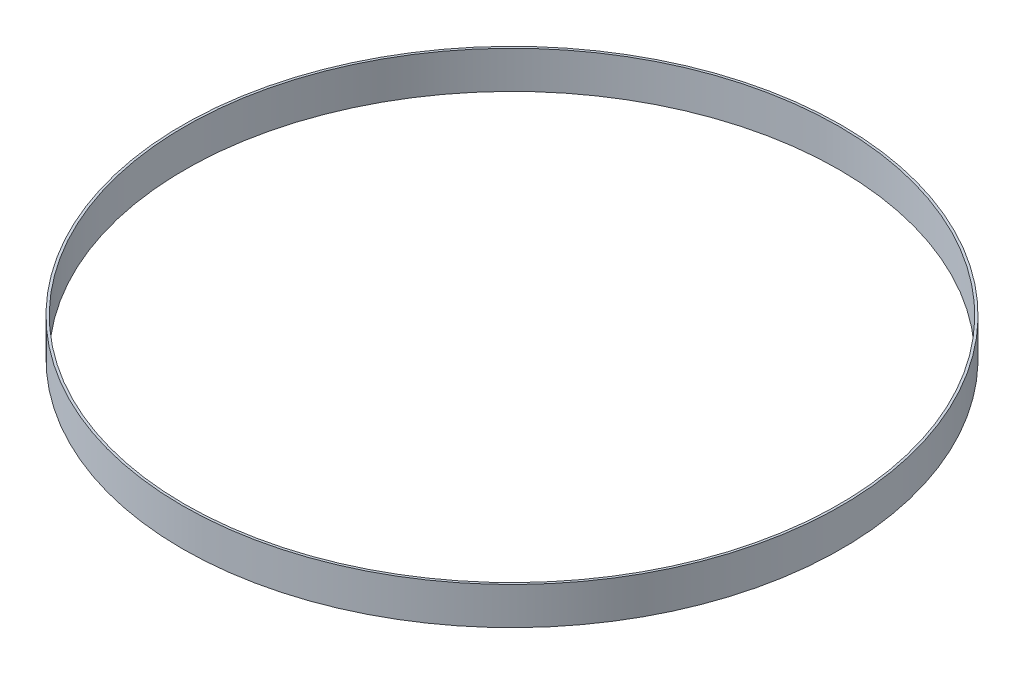
SolidWorks part; units mm, degrees
ref_plane "Front Plane" through (0, 0, 0) normal (0, 0, 1) x (1, 0, 0)
ref_plane "Top Plane" through (0, 0, 0) normal (0, 1, 0) x (1, 0, 0)
ref_plane "Right Plane" through (0, 0, 0) normal (1, 0, 0) x (0, 0, -1)
sketch "Sketch2" plane through (0, 0, 0) normal (0, 1, 0) x (1, 0, 0)
  circle A0 centre (0, 0) radius 70
  circle A1 centre (0, 0) radius 70.5
  dimension "D1" = 140
  dimension "D2" = 141
extrude "Boss-Extrude1" add sketch "Sketch2" along normal blind 8
